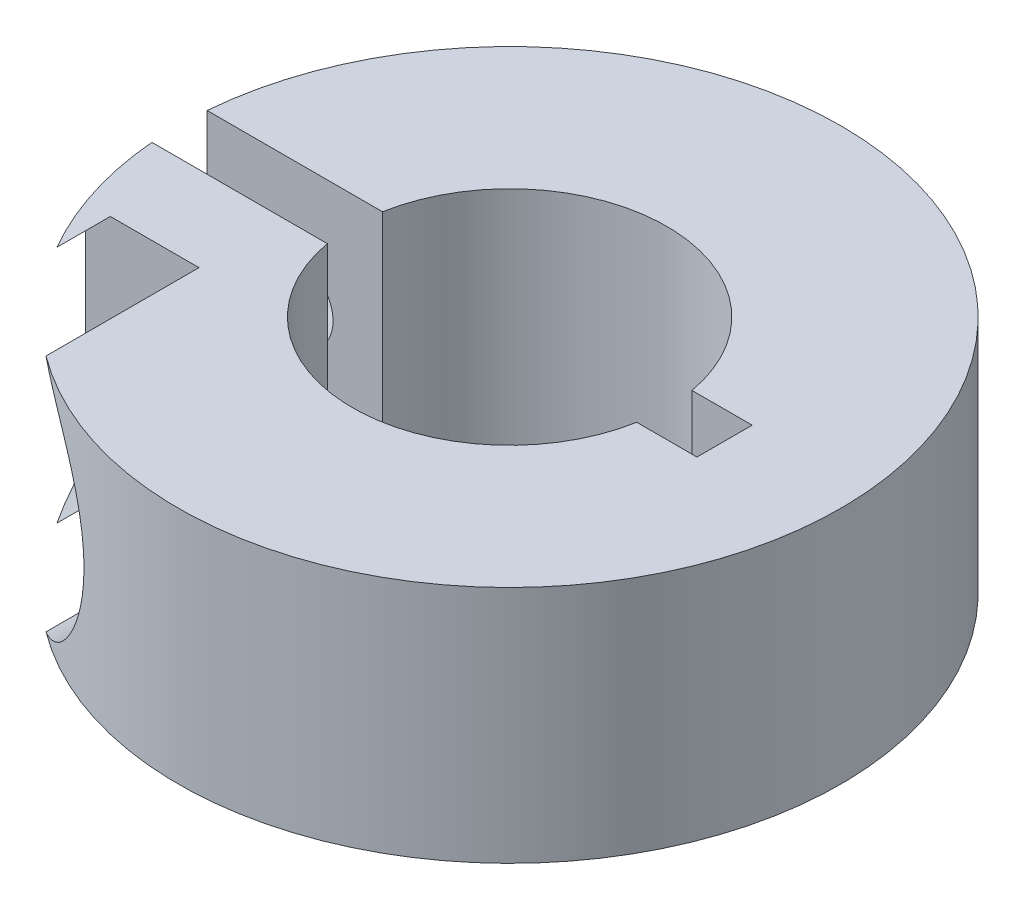
SolidWorks part; units mm, degrees
ref_plane "Front Plane" through (0, 0, 0) normal (0, 0, 1) x (1, 0, 0)
ref_plane "Top Plane" through (0, 0, 0) normal (0, 1, 0) x (1, 0, 0)
ref_plane "Right Plane" through (0, 0, 0) normal (1, 0, 0) x (0, 0, -1)
sketch "Sketch1" plane through (0, 0, 0) normal (0, 1, 0) x (1, 0, 0)
  circle A0 centre (0, 0) radius 9.906
  dimension "D1" = 19.812
extrude "Boss-Extrude1" add sketch "Sketch1" along normal blind 7.1437
sketch "Sketch2" plane through (0, 0, 0) normal (0, -1, 0) x (-1, 0, 0)
  circle A0 centre (0, 0) radius 4.699
extrude "Cut-Extrude1" cut sketch "Sketch2" against normal through all
ref_plane "Plane1" through (-9.906, 0, 0) normal (-1, 0, 0) x (0, 0, 1)
sketch "Sketch5" plane through (-9.906, 0, 0) normal (-1, 0, 0) x (0, 0, 1)
  line L0 (0, 0) -> (0, -50000) construction
  line L1 (0, 11.9422) -> (0.8255, 11.9422) construction
  line L3 (0.8255, 11.9422) -> (-0.8255, 11.9422)
  line L4 (0.8255, 11.9422) -> (0.8255, -1.5559)
  line L5 (0.8255, -1.5559) -> (-0.8255, -1.5559)
  line L6 (-0.8255, 11.9422) -> (-0.8255, -1.5559)
  dimension "D1" = 0.8255
  dimension "D2" = 1.651
extrude "Cut-Extrude3" cut sketch "Sketch5" against normal blind 16.3322
sketch "Sketch6" plane through (0, 0, -0.8255) normal (0, 0, 1) x (1, 0, 0)
  line L0 (-4.6259, 7.1437) -> (-9.8715, 0) construction
  line L1 (-9.8715, 7.1437) -> (-4.6259, 0) construction
  line L2 (-4.6259, 7.1437) -> (-9.8715, 7.1437) construction
  circle A0 centre (-7.2487, 3.5719) radius 1.143
extrude "Cut-Extrude4" cut sketch "Sketch6" against normal through all and the other way through all
ref_plane "Plane2" through (0, 0, 3.3655) normal (0, 0, -1) x (-1, 0, 0)
sketch "Sketch8" plane through (0, 0, 3.3655) normal (0, 0, -1) x (-1, 0, 0)
  circle A0 centre (7.2487, 3.5719) radius 3.81
extrude "Cut-Extrude5" cut sketch "Sketch8" against normal blind 16.3322
